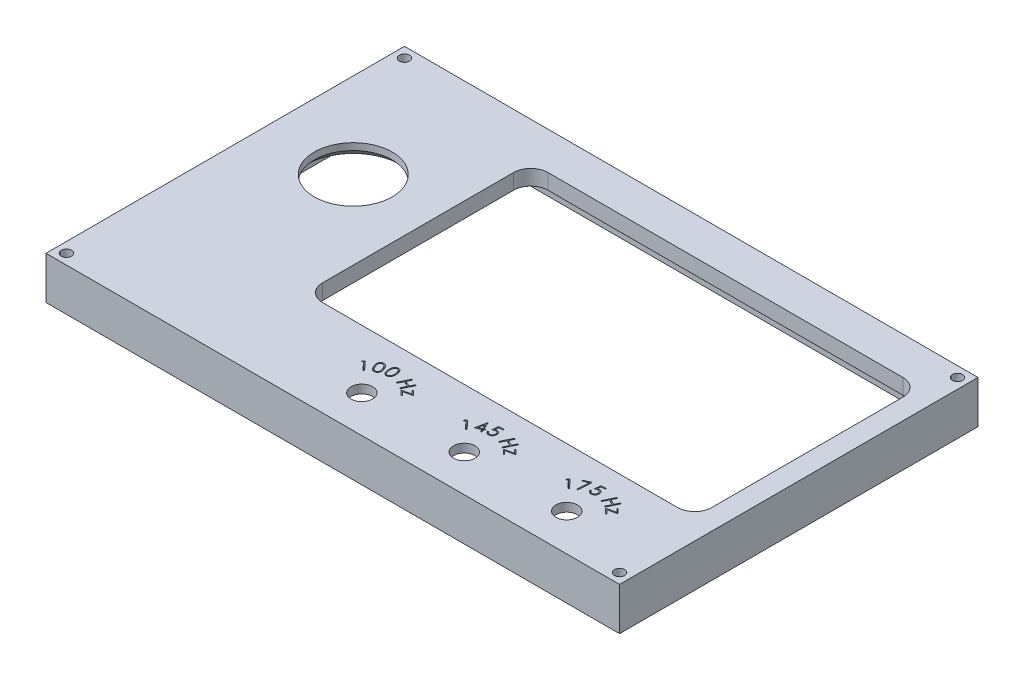
SolidWorks part; units mm, degrees
ref_plane "Front Plane" through (0, 0, 0) normal (0, 0, 1) x (1, 0, 0)
ref_plane "Top Plane" through (0, 0, 0) normal (0, 1, 0) x (1, 0, 0)
ref_plane "Right Plane" through (0, 0, 0) normal (1, 0, 0) x (0, 0, -1)
sketch "Sketch1" plane through (0, 0, 0) normal (0, 1, 0) x (1, 0, 0)
  line L0 (-84, 105) -> (-84, 0) construction
  line L1 (0, 0) -> (-168, 0)
  line L2 (0, 0) -> (0, 105)
  line L3 (0, 105) -> (-168, 105)
  line L4 (-168, 0) -> (-168, 105)
  line L5 (0, 52.5) -> (-168, 52.5) construction
  circle A0 centre (-165, 102) radius 1.5
  circle A1 centre (-3, 102) radius 1.5
  circle A2 centre (-3, 3) radius 1.5
  circle A3 centre (-165, 3) radius 1.5
  dimension "D3" = 3
  dimension "D1" = 168
  dimension "D2" = 105
  dimension "D4" = 3
  dimension "D5" = 3
extrude "Boss-Extrude1" add sketch "Sketch1" along normal blind 12.5
shell "Shell1" thickness 4.5
sketch "Sketch3" plane through (0, 12.5, 0) normal (0, 1, 0) x (1, 0, 0)
  line L0 (-159.1905, 4.5) -> (-8.8095, 4.5) construction
  line L3 (-3, 20) -> (-128, 20) construction
  line L4 (-128, 102) -> (-128, 20) construction
  line L5 (0, 0) -> (0, 105) construction
  line L6 (0, 105) -> (-168, 105) construction
  line L7 (-128, 102) -> (-3, 102) construction
  line L8 (-3, 102) -> (-3, 20) construction
  line L10 (-11, 28) -> (-115, 28)
  line L11 (-6, 33) -> (-6, 89)
  line L12 (-11, 94) -> (-115, 94)
  line L13 (-120, 33) -> (-120, 89)
  line L15 (-80.5083, 4.5) -> (-92.1583, 4.5) construction
  line L16 (-80.5083, 4.5) -> (-80.5083, 17.2) construction
  line L17 (-80.5083, 17.2) -> (-92.1583, 17.2) construction
  line L18 (-92.1583, 4.5) -> (-92.1583, 17.2) construction
  line L19 (-130, 48) -> (-156, 48) construction
  line L20 (-130, 48) -> (-130, 82) construction
  line L21 (-130, 82) -> (-156, 82) construction
  line L22 (-156, 48) -> (-156, 82) construction
  circle A0 centre (-143, 65) radius 11.4
  circle A1 centre (-86.3333, 10.85) radius 3.15
  circle A2 centre (-56.3333, 10.85) radius 3.15
  circle A3 centre (-26.3333, 10.85) radius 3.15
  arc A4 (-115, 28) -> (-120, 33) centre (-115, 33) cw
  arc A5 (-11, 28) -> (-6, 33) centre (-11, 33) ccw
  arc A6 (-6, 89) -> (-11, 94) centre (-11, 89) ccw
  arc A7 (-115, 94) -> (-120, 89) centre (-115, 89) ccw
  point P4 (-92.1583, 10.85)
  point P9 (-86.3333, 4.5)
  point P42 (-156, 65)
  point P44 (-143, 82)
  dimension "D9" = 22.8
  dimension "D12" = 6.3
  dimension "D18" = 5
  dimension "D1" = 3
  dimension "D2" = 3
  dimension "D3" = 82
  dimension "D4" = 125
  dimension "D5" = 3
  dimension "D6" = 8
  dimension "D7" = 8
  dimension "D8" = 8
  dimension "D10" = 15
  dimension "D11" = 40
  dimension "D13" = 12.7
  dimension "D14" = 11.65
  dimension "D15" = 41.6667
  dimension "D17" = 30
  dimension "D19" = 26
  dimension "D20" = 34
  dimension "D16" = 3
extrude "Cut-Extrude1" cut sketch "Sketch3" against normal through all
sketch "Sketch5" plane through (0, 8, 0) normal (0, -1, 0) x (1, 0, 0)
  line L0 (-132.8, -50.3) -> (-132.8, -53.3) construction
  line L1 (-130, -82) -> (-156, -82) construction
  line L2 (-130, -82) -> (-130, -48) construction
  line L3 (-130, -48) -> (-156, -48) construction
  line L4 (-156, -82) -> (-156, -48) construction
  line L5 (-131.3, -51.8) -> (-134.3, -51.8) construction
  line L6 (-153.2, -77.5) -> (-153.2, -80.5) construction
  line L7 (-151.7, -79) -> (-154.7, -79) construction
  line L8 (-143, -48) -> (-143, -82) construction
  circle A0 centre (-143, -65) radius 11.4 construction
  circle A1 centre (-143, -65) radius 11.4 construction
  circle A2 centre (-132.8, -51.8) radius 1.5
  circle A3 centre (-153.2, -79) radius 1.5
  circle A4 centre (-132.8, -79) radius 1.5
  circle A5 centre (-153.2, -51.8) radius 1.5
  point P7 (-156, -65)
  point P8 (-143, -48)
  dimension "D3" = 3
  dimension "D6" = 3
  dimension "D1" = 26
  dimension "D2" = 34
  dimension "D4" = 2.3
  dimension "D5" = 1.3
  dimension "D7" = 1.5
  dimension "D8" = 1.3
extrude "Cut-Extrude3" cut sketch "Sketch5" against normal offset from surface (1.5 mm away) 3 up to face at (-143, 12.5, -53.6)
sketch "Sketch4" plane through (0, 12.5, 0) normal (0, 1, 0) x (1, 0, 0)
  line L0 (-71.3333, 28) -> (-71.3333, 0) construction
  line L1 (-115, 28) -> (-11, 28) construction
  line L2 (-168, 0) -> (0, 0) construction
  line L3 (-41.3333, 28) -> (-41.3333, 0) construction
  line L4 (-86.3333, 10.85) -> (-56.3333, 10.85) construction
  line L5 (-56.3333, 10.85) -> (-26.3333, 10.85) construction
  arc A0 (-93.8333, 14.0394) -> (-78.8333, 14.0394) centre (-86.3333, 10.85) cw construction
  circle A1 centre (-86.3333, 10.85) radius 3.15 construction
  arc A2 (-48.8333, 14.0394) -> (-63.8333, 14.0394) centre (-56.3333, 10.85) ccw construction
  arc A3 (-33.8333, 14.0394) -> (-18.8333, 14.0394) centre (-26.3333, 10.85) cw construction
  text T0 "100 Hz"
  text T1 "145 Hz"
  text T2 "175 Hz"
  point P18 (-71.3333, 10.85)
  point P19 (-41.3333, 10.85)
  dimension "D1" = 5
  dimension "D2" = 15
extrude "Cut-Extrude2" cut sketch "Sketch4" against normal offset from surface (3.5 mm away) 1 up to face at (-153.2, 8, -50.3)
chamfer "Chamfer1" distance 2.5 angle 45 1 edges at (-143, 8, -53.6)
sketch "Sketch6" plane through (0, 12.5, 0) normal (0, 1, 0) x (1, 0, 0)
  line L0 (-168, 105) -> (-168, 0) construction
  line L1 (-129.1, 46.0172) -> (-168, 46.0172)
  line L2 (-129.1, 46.0172) -> (-129.1, 80.9359)
  line L3 (-129.1, 80.9359) -> (-168, 80.9359)
  line L4 (-168, 46.0172) -> (-168, 80.9359)
  line L5 (-8.8095, 100.5) -> (-159.1905, 100.5) construction
  circle A0 centre (-143, 65) radius 13.9 construction
  dimension "D1" = 34.9186
  dimension "D2" = 19.5641
extrude "Cut-Extrude4" [suppressed] cut sketch "Sketch6" against normal through all flip side to cut
sketch "Sketch7" plane through (0, 8, 0) normal (0, -1, 0) x (1, 0, 0)
  line L0 (-89.4833, -10.85) -> (-83.1833, -10.85) construction
  line L1 (-80.1833, -17.205) -> (-92.4833, -17.205)
  line L2 (-80.1833, -17.205) -> (-80.1833, -4.495)
  line L3 (-80.1833, -4.495) -> (-92.4833, -4.495)
  line L4 (-92.4833, -17.205) -> (-92.4833, -4.495)
  line L5 (-50.1833, -17.205) -> (-50.1833, -4.495)
  line L6 (-50.1833, -17.205) -> (-62.4833, -17.205)
  line L7 (-62.4833, -17.205) -> (-62.4833, -4.495)
  line L8 (-50.1833, -4.495) -> (-62.4833, -4.495)
  line L9 (-20.1833, -17.205) -> (-20.1833, -4.495)
  line L10 (-20.1833, -17.205) -> (-32.4833, -17.205)
  line L11 (-32.4833, -17.205) -> (-32.4833, -4.495)
  line L12 (-20.1833, -4.495) -> (-32.4833, -4.495)
  circle A0 centre (-86.3333, -10.85) radius 3.15 construction
  point P9 (-92.4833, -10.85)
  point P10 (-86.3333, -10.85)
  point P11 (-86.3333, -4.495)
  dimension "D1" = 12.3
  dimension "D2" = 12.71
  dimension "D4" = 17.7
  dimension "D3" = 3
extrude "Cut-Extrude5" cut sketch "Sketch7" against normal blind 2
